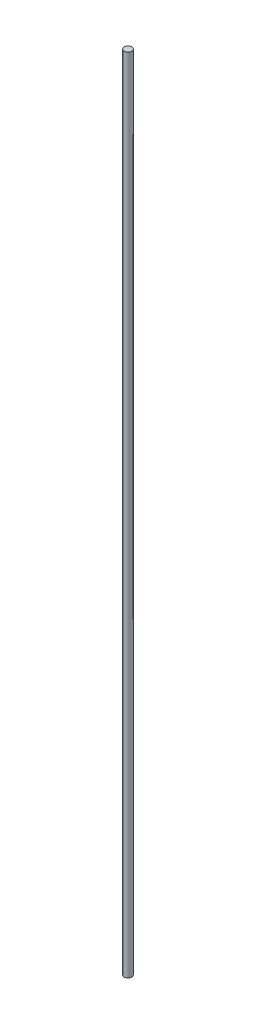
SolidWorks part; units mm, degrees
ref_plane "Plan de face" through (0, 0, 0) normal (0, 0, 1) x (1, 0, 0)
ref_plane "Plan de dessus" through (0, 0, 0) normal (0, 1, 0) x (1, 0, 0)
ref_plane "Plan de droite" through (0, 0, 0) normal (1, 0, 0) x (0, 0, -1)
sketch "Esquisse1" plane through (0, 0, 0) normal (0, 1, 0) x (1, 0, 0)
  circle A0 centre (0, 0) radius 1.5
  dimension "D1" = 3
extrude "Extrusion1" add sketch "Esquisse1" along normal blind 320
